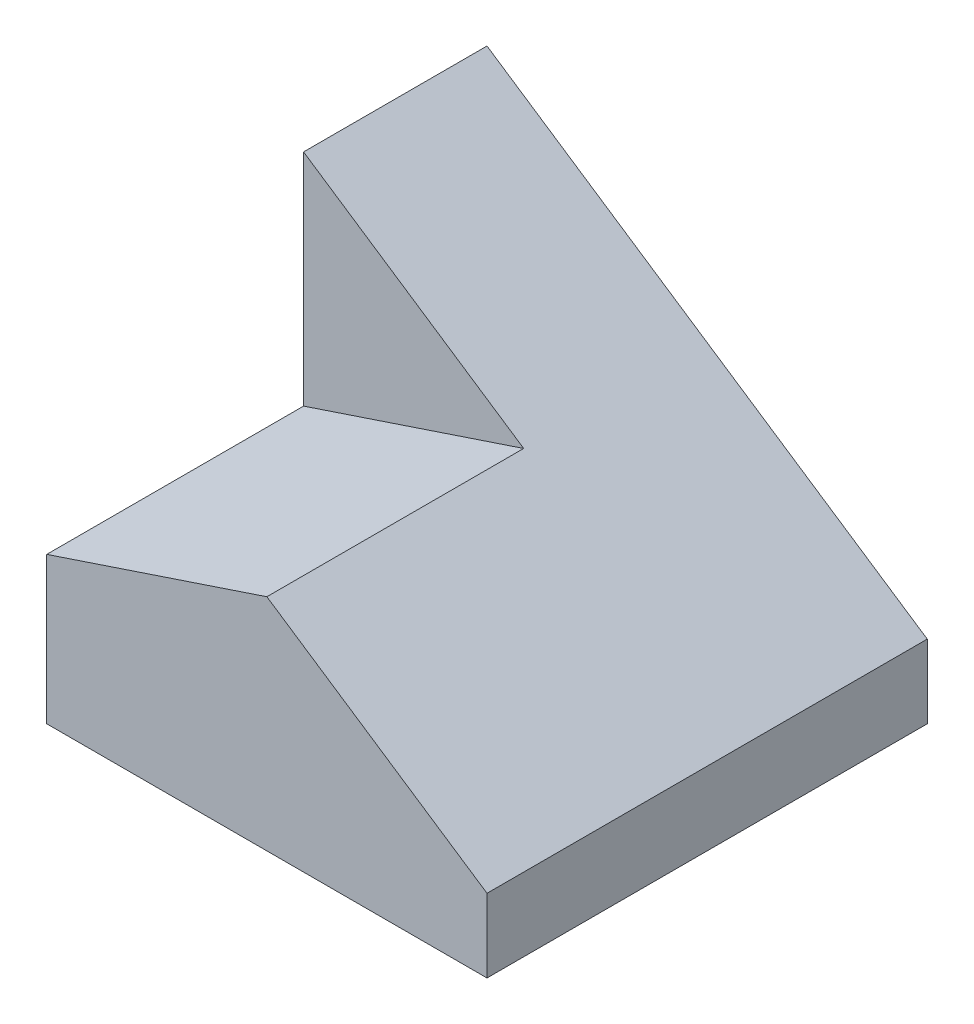
SolidWorks part; units mm, degrees
ref_plane "Front" through (0, 0, 0) normal (0, 0, 1) x (1, 0, 0)
ref_plane "Top" through (0, 0, 0) normal (0, 1, 0) x (1, 0, 0)
ref_plane "Right" through (0, 0, 0) normal (1, 0, 0) x (0, 0, -1)
sketch "Sketch1" plane through (0, 0, 0) normal (0, 1, 0) x (1, 0, 0)
  line L1 (-3, -3) -> (3, -3)
  line L2 (-3, -3) -> (-3, 3)
  line L3 (-3, 3) -> (3, 3)
  line L4 (3, -3) -> (3, 3)
  line L5 (-3, -3) -> (3, 3) construction
  line L6 (-3, 3) -> (3, -3) construction
  point P0 (0, 0)
  dimension "D1" = 6
  dimension "D2" = 6
extrude "Boss-Extrude1" add sketch "Sketch1" along normal blind 5
sketch "Sketch10" plane through (0, 0, 3) normal (0, 0, 1) x (1, 0, 0)
  line L0 (-3, 5) -> (3, 1)
  line L4 (-3, 0) -> (3, 0)
  line L5 (3, 0) -> (3, 5)
  line L6 (3, 5) -> (-3, 5)
  line L7 (-3, 5) -> (-3, 0)
  line L8 (-3, 0) -> (3, 0)
  line L9 (3, 0) -> (3, 5)
  line L10 (3, 5) -> (-3, 5)
  line L11 (-3, 5) -> (-3, 0)
  line M6 (3, 0) -> (3, 5)
  line M7 (3, 5) -> (-3, 5)
  dimension "D2" = 1
  dimension "D1" = 0
extrude "Cut-Extrude7" cut sketch "Sketch10" against normal blind 8 contours L0 M7 M6
sketch "Sketch11" plane through (0, 0, 3) normal (0, 0, 1) x (1, 0, 0)
  line L0 (-3, 2) -> (0, 3)
  line L4 (3, 0) -> (3, 1)
  line L5 (3, 1) -> (-3, 5)
  line L6 (-3, 5) -> (-3, 0)
  line L7 (-3, 0) -> (3, 0)
  line L8 (3, 0) -> (3, 1)
  line L9 (3, 1) -> (-3, 5)
  line L10 (-3, 5) -> (-3, 0)
  line L11 (-3, 0) -> (3, 0)
  line M6 (3, 1) -> (-3, 5)
  line M7 (-3, 5) -> (-3, 0)
  dimension "D2" = 2
  dimension "D3" = 3
  dimension "D1" = 0
extrude "Cut-Extrude8" cut sketch "Sketch11" against normal blind 3.5 contours L0 M7 M6
